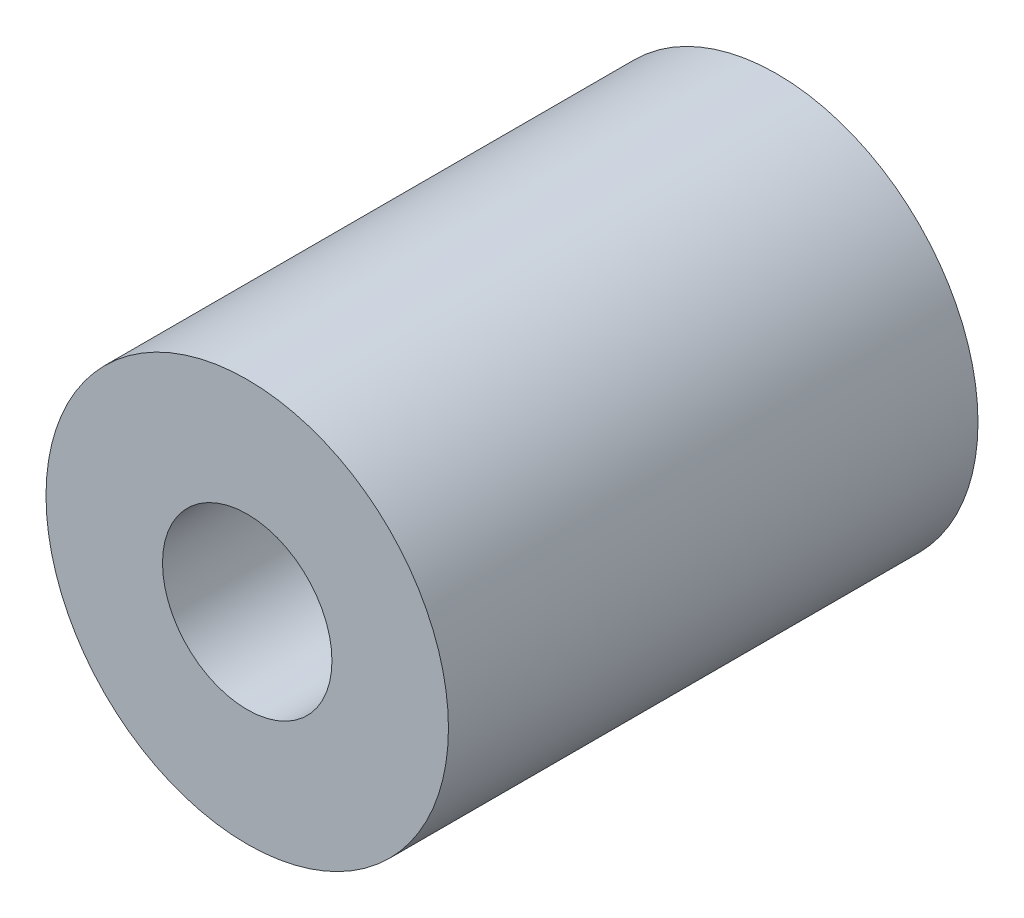
SolidWorks part; units mm, degrees
ref_plane "前视基准面" through (0, 0, 0) normal (0, 0, 1) x (1, 0, 0)
ref_plane "上视基准面" through (0, 0, 0) normal (0, 1, 0) x (1, 0, 0)
ref_plane "右视基准面" through (0, 0, 0) normal (1, 0, 0) x (0, 0, -1)
sketch "草图1" plane through (0, 0, 0) normal (0, 0, 1) x (1, 0, 0)
  circle A0 centre (0, 0) radius 9.5
  dimension "D1" = 19
extrude "凸台-拉伸1" add sketch "草图1" along normal blind 25
sketch "草图2" plane through (0, 0, 25) normal (0, 0, 1) x (1, 0, 0)
  circle A0 centre (0, 0) radius 4
extrude "切除-拉伸1" cut sketch "草图2" against normal blind 12.5
sketch "草图3" plane through (0, 0, 0) normal (0, 0, -1) x (-1, 0, 0)
  circle A0 centre (0, 0) radius 3
extrude "切除-拉伸2" cut sketch "草图3" against normal blind 12.5
